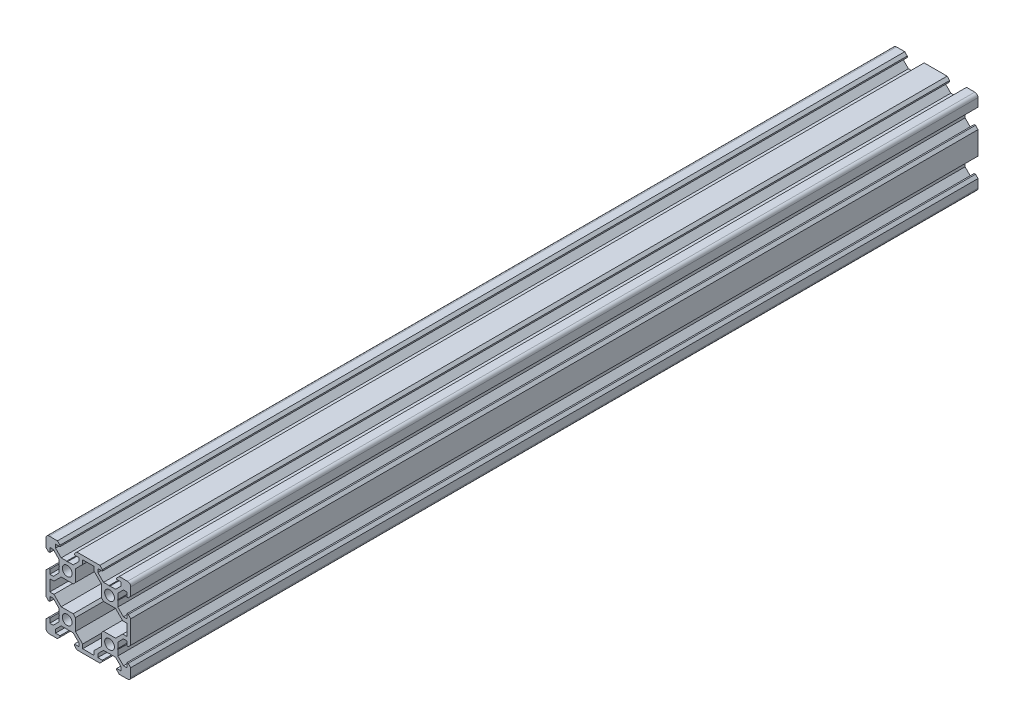
SolidWorks part; units mm, degrees
material "6061-T6 (SS)"
ref_plane "Front Plane" through (0, 0, 0) normal (0, 0, 1) x (1, 0, 0)
ref_plane "Top Plane" through (0, 0, 0) normal (0, 1, 0) x (1, 0, 0)
ref_plane "Right Plane" through (0, 0, 0) normal (1, 0, 0) x (0, 0, -1)
sketch "Sketch1" plane through (0, 0, 0) normal (0, 0, 1) x (1, 0, 0)
  line L1 (18.5, -20) -> (-18.5, -20)
  line L2 (20, -18.5) -> (20, 18.5)
  line L3 (18.5, 20) -> (-18.5, 20)
  line L4 (-20, -18.5) -> (-20, 18.5)
  line L5 (20, -20) -> (-20, 20) construction
  line L6 (20, 20) -> (-20, -20) construction
  circle A0 centre (-10, 10) radius 2.3
  circle A1 centre (10, -10) radius 2.3
  circle A2 centre (10, 10) radius 2.3
  circle A3 centre (-10, -10) radius 2.3
  arc A4 (-18.5, -20) -> (-20, -18.5) centre (-18.5, -18.5) cw
  arc A5 (18.5, -20) -> (20, -18.5) centre (18.5, -18.5) ccw
  arc A6 (20, 18.5) -> (18.5, 20) centre (18.5, 18.5) ccw
  arc A7 (-18.5, 20) -> (-20, 18.5) centre (-18.5, 18.5) ccw
  point P0 (0, 0)
  line B0 (-10, 10) -> (-10, 20) construction
  line B1 (-10, 13.69) -> (-10.21, 13.9)
  line B2 (-10.21, 13.9) -> (-12.8393, 13.9)
  line B3 (-12.8393, 13.9) -> (-15.5, 16.5607)
  line B4 (-15.5, 16.5607) -> (-15.5, 18.2)
  line B5 (-15.5, 18.2) -> (-13.395, 18.2)
  line B6 (-13.395, 18.2) -> (-13.395, 18.815)
  line B7 (-13.395, 18.815) -> (-14.58, 20)
  line B8 (-14.58, 20) -> (-5.42, 20)
  line B9 (-10, 10) -> (-15.9132, 15.9132) construction
  line B10 (-6.605, 18.815) -> (-5.42, 20)
  line B11 (-6.605, 18.2) -> (-6.605, 18.815)
  line B12 (-4.5, 18.2) -> (-6.605, 18.2)
  line B13 (-4.5, 16.5607) -> (-4.5, 18.2)
  line B14 (-7.1607, 13.9) -> (-4.5, 16.5607)
  line B15 (-9.79, 13.9) -> (-7.1607, 13.9)
  line B16 (-10, 13.69) -> (-9.79, 13.9)
  line B17 (10, 10) -> (10, 20) construction
  line B18 (10, 13.69) -> (9.79, 13.9)
  line B19 (9.79, 13.9) -> (7.1607, 13.9)
  line B20 (7.1607, 13.9) -> (4.5, 16.5607)
  line B21 (4.5, 16.5607) -> (4.5, 18.2)
  line B22 (4.5, 18.2) -> (6.605, 18.2)
  line B23 (6.605, 18.2) -> (6.605, 18.815)
  line B24 (6.605, 18.815) -> (5.42, 20)
  line B25 (5.42, 20) -> (14.58, 20)
  line B26 (10, 10) -> (4.0868, 15.9132) construction
  line B27 (13.395, 18.815) -> (14.58, 20)
  line B28 (13.395, 18.2) -> (13.395, 18.815)
  line B29 (15.5, 18.2) -> (13.395, 18.2)
  line B30 (15.5, 16.5607) -> (15.5, 18.2)
  line B31 (12.8393, 13.9) -> (15.5, 16.5607)
  line B32 (10.21, 13.9) -> (12.8393, 13.9)
  line B33 (10, 13.69) -> (10.21, 13.9)
  line B34 (-10, 10) -> (-20, 10) construction
  line B35 (-13.69, 10) -> (-13.9, 9.79)
  line B36 (-13.9, 9.79) -> (-13.9, 7.1607)
  line B37 (-13.9, 7.1607) -> (-16.5607, 4.5)
  line B38 (-16.5607, 4.5) -> (-18.2, 4.5)
  line B39 (-18.2, 4.5) -> (-18.2, 6.605)
  line B40 (-18.2, 6.605) -> (-18.815, 6.605)
  line B41 (-18.815, 6.605) -> (-20, 5.42)
  line B42 (-20, 5.42) -> (-20, 14.58)
  line B43 (-10, 10) -> (-15.9132, 4.0868) construction
  line B44 (-18.815, 13.395) -> (-20, 14.58)
  line B45 (-18.2, 13.395) -> (-18.815, 13.395)
  line B46 (-18.2, 15.5) -> (-18.2, 13.395)
  line B47 (-16.5607, 15.5) -> (-18.2, 15.5)
  line B48 (-13.9, 12.8393) -> (-16.5607, 15.5)
  line B49 (-13.9, 10.21) -> (-13.9, 12.8393)
  line B50 (-13.69, 10) -> (-13.9, 10.21)
  line B51 (-10, -10) -> (-20, -10) construction
  line B52 (-13.69, -10) -> (-13.9, -10.21)
  line B53 (-13.9, -10.21) -> (-13.9, -12.8393)
  line B54 (-13.9, -12.8393) -> (-16.5607, -15.5)
  line B55 (-16.5607, -15.5) -> (-18.2, -15.5)
  line B56 (-18.2, -15.5) -> (-18.2, -13.395)
  line B57 (-18.2, -13.395) -> (-18.815, -13.395)
  line B58 (-18.815, -13.395) -> (-20, -14.58)
  line B59 (-20, -14.58) -> (-20, -5.42)
  line B60 (-10, -10) -> (-15.9132, -15.9132) construction
  line B61 (-18.815, -6.605) -> (-20, -5.42)
  line B62 (-18.2, -6.605) -> (-18.815, -6.605)
  line B63 (-18.2, -4.5) -> (-18.2, -6.605)
  line B64 (-16.5607, -4.5) -> (-18.2, -4.5)
  line B65 (-13.9, -7.1607) -> (-16.5607, -4.5)
  line B66 (-13.9, -9.79) -> (-13.9, -7.1607)
  line B67 (-13.69, -10) -> (-13.9, -9.79)
  line B68 (-10, -10) -> (-10, -20) construction
  line B69 (-10, -13.69) -> (-9.79, -13.9)
  line B70 (-9.79, -13.9) -> (-7.1607, -13.9)
  line B71 (-7.1607, -13.9) -> (-4.5, -16.5607)
  line B72 (-4.5, -16.5607) -> (-4.5, -18.2)
  line B73 (-4.5, -18.2) -> (-6.605, -18.2)
  line B74 (-6.605, -18.2) -> (-6.605, -18.815)
  line B75 (-6.605, -18.815) -> (-5.42, -20)
  line B76 (-5.42, -20) -> (-14.58, -20)
  line B77 (-10, -10) -> (-4.0868, -15.9132) construction
  line B78 (-13.395, -18.815) -> (-14.58, -20)
  line B79 (-13.395, -18.2) -> (-13.395, -18.815)
  line B80 (-15.5, -18.2) -> (-13.395, -18.2)
  line B81 (-15.5, -16.5607) -> (-15.5, -18.2)
  line B82 (-12.8393, -13.9) -> (-15.5, -16.5607)
  line B83 (-10.21, -13.9) -> (-12.8393, -13.9)
  line B84 (-10, -13.69) -> (-10.21, -13.9)
  line B85 (10, -10) -> (10, -20) construction
  line B86 (10, -13.69) -> (10.21, -13.9)
  line B87 (10.21, -13.9) -> (12.8393, -13.9)
  line B88 (12.8393, -13.9) -> (15.5, -16.5607)
  line B89 (15.5, -16.5607) -> (15.5, -18.2)
  line B90 (15.5, -18.2) -> (13.395, -18.2)
  line B91 (13.395, -18.2) -> (13.395, -18.815)
  line B92 (13.395, -18.815) -> (14.58, -20)
  line B93 (14.58, -20) -> (5.42, -20)
  line B94 (10, -10) -> (15.9132, -15.9132) construction
  line B95 (6.605, -18.815) -> (5.42, -20)
  line B96 (6.605, -18.2) -> (6.605, -18.815)
  line B97 (4.5, -18.2) -> (6.605, -18.2)
  line B98 (4.5, -16.5607) -> (4.5, -18.2)
  line B99 (7.1607, -13.9) -> (4.5, -16.5607)
  line B100 (9.79, -13.9) -> (7.1607, -13.9)
  line B101 (10, -13.69) -> (9.79, -13.9)
  line B102 (10, 10) -> (20, 10) construction
  line B103 (13.69, 10) -> (13.9, 10.21)
  line B104 (13.9, 10.21) -> (13.9, 12.8393)
  line B105 (13.9, 12.8393) -> (16.5607, 15.5)
  line B106 (16.5607, 15.5) -> (18.2, 15.5)
  line B107 (18.2, 15.5) -> (18.2, 13.395)
  line B108 (18.2, 13.395) -> (18.815, 13.395)
  line B109 (18.815, 13.395) -> (20, 14.58)
  line B110 (20, 14.58) -> (20, 5.42)
  line B111 (10, 10) -> (15.9132, 15.9132) construction
  line B112 (18.815, 6.605) -> (20, 5.42)
  line B113 (18.2, 6.605) -> (18.815, 6.605)
  line B114 (18.2, 4.5) -> (18.2, 6.605)
  line B115 (16.5607, 4.5) -> (18.2, 4.5)
  line B116 (13.9, 7.1607) -> (16.5607, 4.5)
  line B117 (13.9, 9.79) -> (13.9, 7.1607)
  line B118 (13.69, 10) -> (13.9, 9.79)
  line B119 (10, -10) -> (20, -10) construction
  line B120 (13.69, -10) -> (13.9, -9.79)
  line B121 (13.9, -9.79) -> (13.9, -7.1607)
  line B122 (13.9, -7.1607) -> (16.5607, -4.5)
  line B123 (16.5607, -4.5) -> (18.2, -4.5)
  line B124 (18.2, -4.5) -> (18.2, -6.605)
  line B125 (18.2, -6.605) -> (18.815, -6.605)
  line B126 (18.815, -6.605) -> (20, -5.42)
  line B127 (20, -5.42) -> (20, -14.58)
  line B128 (10, -10) -> (15.9132, -4.0868) construction
  line B129 (18.815, -13.395) -> (20, -14.58)
  line B130 (18.2, -13.395) -> (18.815, -13.395)
  line B131 (18.2, -15.5) -> (18.2, -13.395)
  line B132 (16.5607, -15.5) -> (18.2, -15.5)
  line B133 (13.9, -12.8393) -> (16.5607, -15.5)
  line B134 (13.9, -10.21) -> (13.9, -12.8393)
  line B135 (13.69, -10) -> (13.9, -10.21)
  line B136 (-18.2, -2.7) -> (-18.2, 2.7)
  line B137 (-18.2, 2.7) -> (-16.2393, 2.7)
  line B138 (-16.2393, 2.7) -> (-12.8393, 6.1)
  line B139 (-12.8393, 6.1) -> (-7.1607, 6.1)
  line B140 (-10, 6.1) -> (-10, 0) construction
  line B141 (-10, 0) -> (-18.2, 0) construction
  line B142 (-12.8393, -6.1) -> (-7.1607, -6.1)
  line B143 (-16.2393, -2.7) -> (-12.8393, -6.1)
  line B144 (-18.2, -2.7) -> (-16.2393, -2.7)
  line B145 (-10, 6.1) -> (-10, 10) construction
  line B146 (-10, 10) -> (-15.0927, 4.9073) construction
  line B147 (-10, 10) -> (-6.3747, 6.3747) construction
  line B148 (2.7, 18.2) -> (2.7, 16.2393)
  line B149 (2.7, 16.2393) -> (6.1, 12.8393)
  line B150 (6.1, 12.8393) -> (6.1, 7.1607)
  line B151 (-6.1, 12.8393) -> (-6.1, 7.1607)
  line B152 (-2.7, 16.2393) -> (-6.1, 12.8393)
  line B153 (-2.7, 18.2) -> (-2.7, 16.2393)
  line B154 (2.7, 18.2) -> (-2.7, 18.2)
  line B155 (2.7, -18.2) -> (-2.7, -18.2)
  line B156 (-2.7, -18.2) -> (-2.7, -16.2393)
  line B157 (-2.7, -16.2393) -> (-6.1, -12.8393)
  line B158 (-6.1, -12.8393) -> (-6.1, -7.1607)
  line B159 (6.1, -12.8393) -> (6.1, -7.1607)
  line B160 (2.7, -16.2393) -> (6.1, -12.8393)
  line B161 (2.7, -18.2) -> (2.7, -16.2393)
  line B162 (0, 18.2) -> (0, -18.2) construction
  line B163 (12.8393, -6.1) -> (7.1607, -6.1)
  line B164 (16.2393, -2.7) -> (12.8393, -6.1)
  line B165 (18.2, -2.7) -> (16.2393, -2.7)
  line B166 (18.2, -2.7) -> (18.2, 2.7)
  line B167 (18.2, 2.7) -> (16.2393, 2.7)
  line B168 (16.2393, 2.7) -> (12.8393, 6.1)
  line B169 (12.8393, 6.1) -> (7.1607, 6.1)
  line B170 (-7.1607, 6.1) -> (-6.1, 7.1607)
  line B171 (6.1, 7.1607) -> (7.1607, 6.1)
  line B172 (7.1607, -6.1) -> (6.1, -7.1607)
  line B173 (-6.1, -7.1607) -> (-7.1607, -6.1)
  dimension "D4" = 4.6
  dimension "D5" = 1.5
  dimension "D1" = 40
  dimension "D2" = 10
  dimension "D3" = 10
sketch_block_instance "V Slot 2-1"
sketch_block "V Slot 2" parameters "D1"=10, "D2"=11, "D3"=4.3, "D4"=1.8, "D5"=0.21, "D6"=45, "D7"=9.16, "D8"=1.5, "D9"=6.79
sketch_block_instance "V Slot 2-2"
sketch_block_instance "V Slot 2-3"
sketch_block_instance "V Slot 2-4"
sketch_block_instance "V Slot 2-5"
sketch_block_instance "V Slot 2-6"
sketch_block_instance "V Slot 2-7"
sketch_block_instance "V Slot 2-8"
sketch_block_instance "Center Cutout 2-1"
sketch_block "Center Cutout 2" parameters "D1"=5.4, "D2"=12.2, "D3"=8.2, "D4"=45, "D5"=10, "D6"=1.5
extrude "Boss-Extrude1" add sketch "Sketch1" along normal blind 400 contours B135 B120 B121 B122 B123 B124 B125 B126 L2 B112 B113 B114 B115 B116 B117 B118 B103 B104 B105 B106 B107 B108 B109 A6 L3 B27 B28 B29 B30 B31 B32 B33 B18 B19 B20 B21 B22 B23 B24 B10 B11 B12 B13 B14 B15 B16 B1 B2 B3
